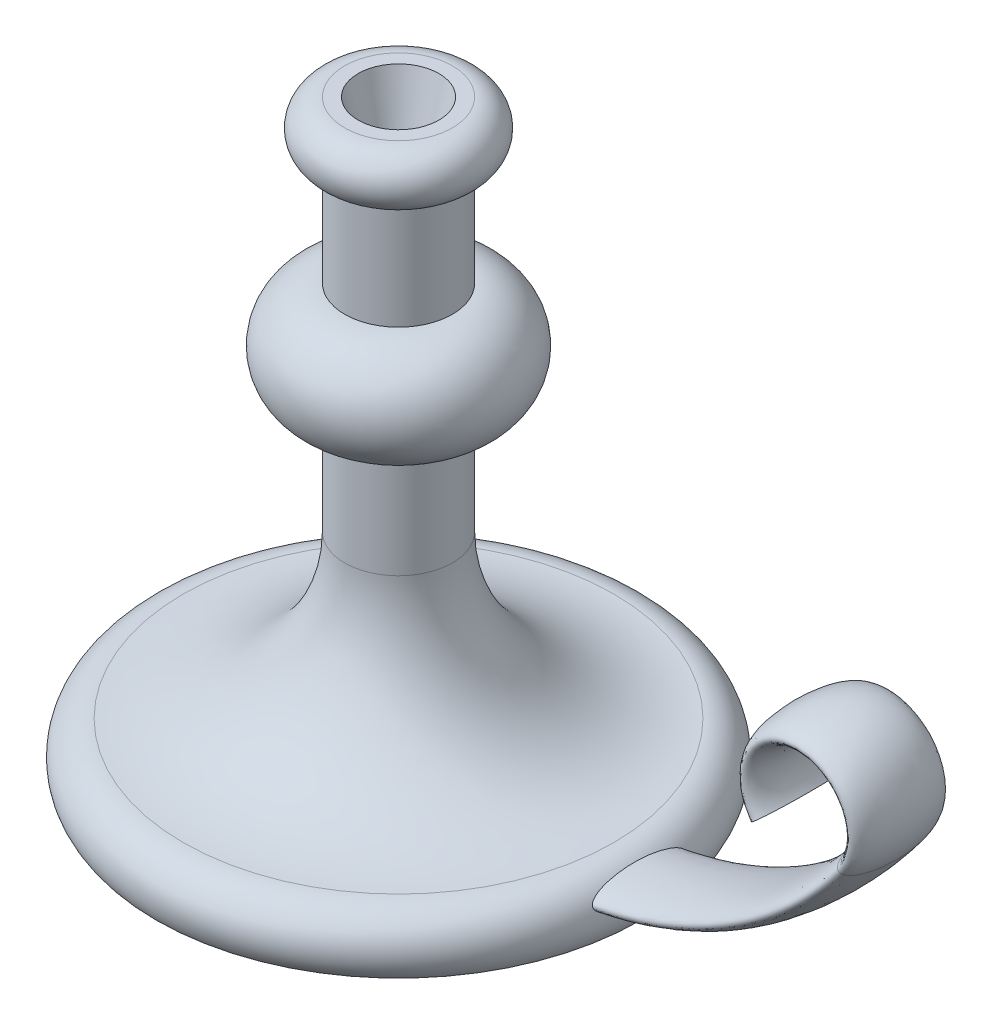
SolidWorks part; units mm, degrees
ref_plane "Płaszczyzna przednia" through (0, 0, 0) normal (0, 0, 1) x (1, 0, 0)
ref_plane "Płaszczyzna górna" through (0, 0, 0) normal (0, 1, 0) x (1, 0, 0)
ref_plane "Płaszczyzna prawa" through (0, 0, 0) normal (1, 0, 0) x (0, 0, -1)
sketch "Szkic1" plane through (0, 0, 0) normal (0, 0, 1) x (1, 0, 0)
  line L0 (0, 0) -> (90, 0)
  line L1 (20, 80) -> (20, 120)
  line L2 (20, 160) -> (20, 200)
  line L3 (20, 220) -> (0, 220)
  line L4 (0, 220) -> (0, 0)
  arc A1 (80, 20) -> (20, 80) centre (80, 80) cw
  arc A2 (20, 120) -> (20, 160) centre (20, 140) ccw
  arc A3 (20, 200) -> (20, 220) centre (20, 210) ccw
  arc A4 (90, 0) -> (80, 20) centre (80, 7.5) ccw
  dimension "D9" = 12.5
  dimension "D1" = 20
  dimension "D2" = 90
  dimension "D3" = 60
  dimension "D4" = 220
  dimension "D5" = 80
  dimension "D6" = 10
  dimension "D7" = 20
  dimension "D8" = 40
revolve "Obrót1" add sketch "Szkic1" angle 360 about L4
sketch "Szkic4" plane through (0, 0, 0) normal (0, 0, 1) x (1, 0, 0)
  line L0 (0, 10) -> (61.0496, 10)
  arc A0 (61.0496, 10) -> (181.0496, 70) centre (61.0496, 160) ccw
  arc A1 (181.0496, 70) -> (149.0496, 70) centre (165.0496, 82) ccw
  dimension "D2" = 61.0496
  dimension "D4" = 150
  dimension "D5" = 20
  dimension "D1" = 60
  dimension "D3" = 10
sketch "Szkic5" plane through (0, 0, 0) normal (1, 0, 0) x (0, 0, -1)
  line L0 (0, 70) -> (0, 10) construction
  ellipse E0 centre (0, 10) end of major axis (17.5, 10) minor radius 5
  point P1 (0, 0)
  point P7 (0, 0)
  dimension "D1" = 35
  dimension "D2" = 10
sweep "Wyciągnięcie po ścieżce1" add profiles "Szkic5" path "Szkic4"
sketch "Szkic10" plane through (0, 220, 0) normal (0, 1, 0) x (1, 0, 0)
  circle A0 centre (0, 0) radius 15
  dimension "D1" = 30
extrude "Wytnij-wyciągnięcie1" cut sketch "Szkic10" against normal blind 25 draft 15
